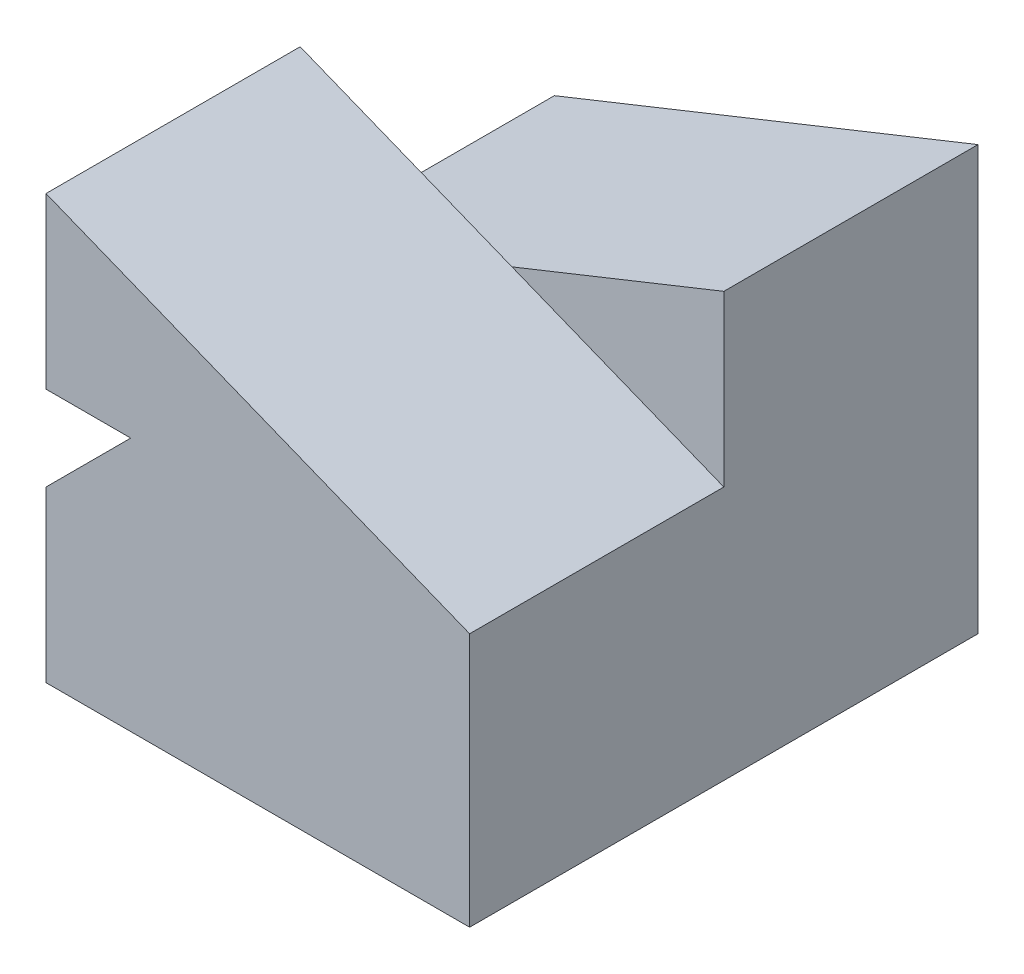
SolidWorks part; units mm, degrees
ref_plane "Front Plane" through (0, 0, 0) normal (0, 0, 1) x (1, 0, 0)
ref_plane "Top Plane" through (0, 0, 0) normal (0, 1, 0) x (1, 0, 0)
ref_plane "Right Plane" through (0, 0, 0) normal (1, 0, 0) x (0, 0, -1)
sketch "Sketch1" plane through (0, 0, 0) normal (0, 0, 1) x (1, 0, 0)
  line L0 (-25, 0) -> (0, 0)
  line L1 (0, 0) -> (0, 15)
  line L2 (0, 15) -> (-20, 15)
  line L3 (-20, 15) -> (-25, 10)
  line L4 (-25, 10) -> (-25, 0)
  dimension "D1" = 15
  dimension "D2" = 25
  dimension "D3" = 20
  dimension "D4" = 10
extrude "Boss-Extrude1" add sketch "Sketch1" along normal blind 15
sketch "Sketch2" plane through (0, 0, 0) normal (0, 0, -1) x (-1, 0, 0)
  line L0 (25, 25) -> (25, 15)
  line L1 (0, 15) -> (20, 15) construction
  line L2 (25, 15) -> (0, 15)
  line L3 (0, 15) -> (25, 25)
  dimension "D1" = 10
  dimension "D2" = 25
extrude "Boss-Extrude2" add sketch "Sketch2" against normal blind 15
sketch "Sketch6" plane through (0, 0, 0) normal (0, 0, -1) x (-1, 0, 0)
  line L0 (0, 15) -> (25, 15)
  line L1 (0, 0) -> (0, 15) construction
  line L2 (25, 10) -> (25, 0) construction
  line L3 (25, 15) -> (25, 0)
  line L4 (25, 0) -> (0, 0)
  line L5 (0, 0) -> (0, 15)
  dimension "D1" = 15
extrude "Boss-Extrude7" add sketch "Sketch6" along normal blind 15 separate body
sketch "Sketch7" plane through (0, 0, 0) normal (0, 0, -1) x (-1, 0, 0)
  line L0 (0, 15) -> (0, 25)
  line L1 (0, 25) -> (25, 15)
  line L2 (25, 15) -> (0, 15)
  dimension "D1" = 10
extrude "Boss-Extrude8" add sketch "Sketch7" along normal blind 15
